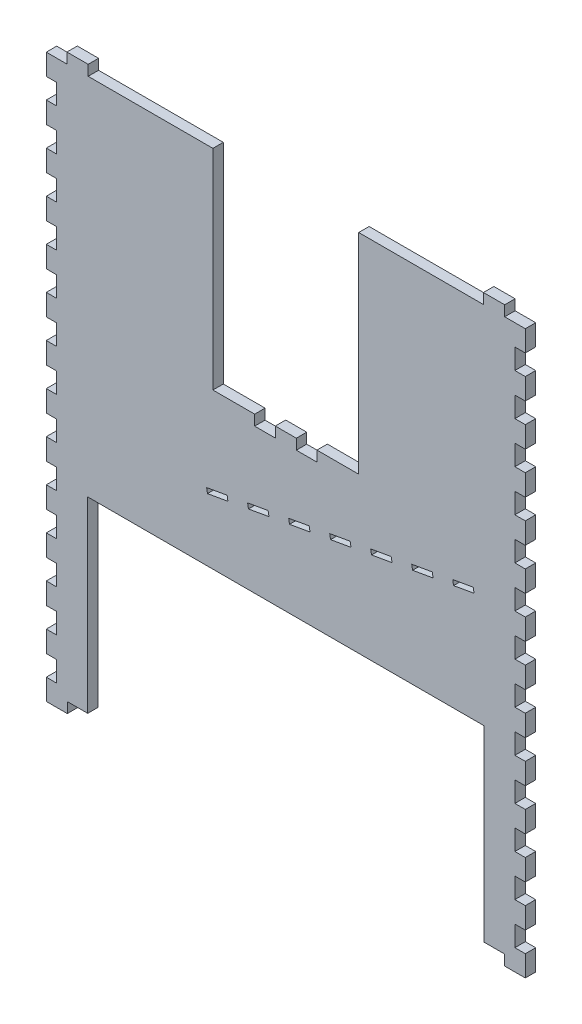
SolidWorks part; units mm, degrees
ref_plane "Front Plane" through (0, 0, 0) normal (0, 0, 1) x (1, 0, 0)
ref_plane "Top Plane" through (0, 0, 0) normal (0, 1, 0) x (1, 0, 0)
ref_plane "Right Plane" through (0, 0, 0) normal (1, 0, 0) x (0, 0, -1)
sketch "Sketch1" plane through (0, 0, 0) normal (0, 0, 1) x (1, 0, 0)
  line L0 (0, 0) -> (12.573, 0)
  line L1 (12.573, 0) -> (12.573, 6.35)
  line L2 (12.573, 6.35) -> (25.527, 6.35)
  line L3 (25.527, 6.35) -> (25.527, 0)
  line L4 (25.527, 0) -> (266.573, 0) construction
  line L5 (266.573, 0) -> (266.573, 6.35)
  line L6 (266.573, 6.35) -> (279.527, 6.35)
  line L7 (279.527, 6.35) -> (279.527, 0)
  line L8 (279.527, 0) -> (292.1, 0)
  line L9 (0, -12.827) -> (0, 0)
  line L10 (0, -12.827) -> (6.35, -12.827)
  line L11 (6.35, -12.827) -> (6.35, -25.273)
  line L12 (6.35, -25.273) -> (0, -25.273)
  line L13 (0, -25.273) -> (0, -38.227)
  line L14 (0, -38.227) -> (6.35, -38.227)
  line L15 (6.35, -38.227) -> (6.35, -50.673)
  line L16 (6.35, -50.673) -> (0, -50.673)
  line L17 (0, -50.673) -> (0, -63.627)
  line L18 (0, -63.627) -> (6.35, -63.627)
  line L19 (6.35, -63.627) -> (6.35, -76.073)
  line L20 (6.35, -76.073) -> (0, -76.073)
  line L21 (0, -76.073) -> (0, -89.027)
  line L22 (0, -89.027) -> (6.35, -89.027)
  line L23 (6.35, -89.027) -> (6.35, -101.473)
  line L24 (6.35, -101.473) -> (0, -101.473)
  line L25 (0, -101.473) -> (0, -114.427)
  line L26 (0, -114.427) -> (6.35, -114.427)
  line L27 (6.35, -114.427) -> (6.35, -126.873)
  line L28 (6.35, -126.873) -> (0, -126.873)
  line L29 (0, -126.873) -> (0, -139.827)
  line L30 (0, -139.827) -> (6.35, -139.827)
  line L31 (6.35, -139.827) -> (6.35, -152.273)
  line L32 (6.35, -152.273) -> (0, -152.273)
  line L33 (0, -152.273) -> (0, -165.227)
  line L34 (0, -165.227) -> (6.35, -165.227)
  line L35 (6.35, -165.227) -> (6.35, -177.673)
  line L36 (6.35, -177.673) -> (0, -177.673)
  line L37 (0, -177.673) -> (0, -190.627)
  line L38 (0, -190.627) -> (6.35, -190.627)
  line L39 (6.35, -190.627) -> (6.35, -203.073)
  line L40 (6.35, -203.073) -> (0, -203.073)
  line L41 (0, -203.073) -> (0, -216.027)
  line L42 (0, -216.027) -> (6.35, -216.027)
  line L43 (6.35, -216.027) -> (6.35, -228.473)
  line L44 (6.35, -228.473) -> (0, -228.473)
  line L45 (0, -228.473) -> (0, -241.427)
  line L46 (0, -241.427) -> (6.35, -241.427)
  line L47 (6.35, -241.427) -> (6.35, -253.873)
  line L48 (6.35, -253.873) -> (0, -253.873)
  line L49 (0, -253.873) -> (0, -266.827)
  line L50 (0, -266.827) -> (6.35, -266.827)
  line L51 (6.35, -266.827) -> (6.35, -279.273)
  line L52 (6.35, -279.273) -> (0, -279.273)
  line L53 (292.1, 0) -> (292.1, -12.827)
  line L54 (292.1, -12.827) -> (285.75, -12.827)
  line L55 (285.75, -12.827) -> (285.75, -25.273)
  line L56 (285.75, -25.273) -> (292.1, -25.273)
  line L57 (292.1, -25.273) -> (292.1, -38.227)
  line L58 (292.1, -38.227) -> (285.75, -38.227)
  line L59 (0, -342.9) -> (12.827, -342.9)
  line L60 (12.827, -342.9) -> (12.827, -336.55)
  line L61 (12.827, -336.55) -> (25.273, -336.55)
  line L62 (25.273, -336.55) -> (25.273, -342.9) construction
  line L63 (25.273, -342.9) -> (38.227, -342.9) construction
  line L64 (38.227, -342.9) -> (38.227, -336.55) construction
  line L65 (38.227, -336.55) -> (50.673, -336.55) construction
  line L66 (50.673, -336.55) -> (50.673, -342.9) construction
  line L67 (50.673, -342.9) -> (63.627, -342.9) construction
  line L68 (63.627, -342.9) -> (63.627, -336.55) construction
  line L69 (63.627, -336.55) -> (76.073, -336.55) construction
  line L70 (76.073, -336.55) -> (76.073, -342.9) construction
  line L71 (76.073, -342.9) -> (89.027, -342.9) construction
  line L72 (89.027, -342.9) -> (89.027, -336.55) construction
  line L73 (89.027, -336.55) -> (101.473, -336.55) construction
  line L74 (101.473, -336.55) -> (101.473, -342.9) construction
  line L75 (101.473, -342.9) -> (114.427, -342.9) construction
  line L76 (114.427, -342.9) -> (114.427, -336.55) construction
  line L77 (114.427, -336.55) -> (126.873, -336.55) construction
  line L78 (126.873, -336.55) -> (126.873, -342.9) construction
  line L79 (126.873, -342.9) -> (139.827, -342.9) construction
  line L80 (139.827, -342.9) -> (139.827, -336.55) construction
  line L81 (139.827, -336.55) -> (152.273, -336.55) construction
  line L82 (152.273, -336.55) -> (152.273, -342.9) construction
  line L83 (152.273, -342.9) -> (165.227, -342.9) construction
  line L84 (165.227, -342.9) -> (165.227, -336.55) construction
  line L85 (165.227, -336.55) -> (177.673, -336.55) construction
  line L86 (177.673, -336.55) -> (177.673, -342.9) construction
  line L87 (177.673, -342.9) -> (190.627, -342.9) construction
  line L88 (190.627, -342.9) -> (190.627, -336.55) construction
  line L89 (190.627, -336.55) -> (203.073, -336.55) construction
  line L90 (203.073, -336.55) -> (203.073, -342.9) construction
  line L91 (203.073, -342.9) -> (216.027, -342.9) construction
  line L92 (216.027, -342.9) -> (216.027, -336.55) construction
  line L93 (216.027, -336.55) -> (228.473, -336.55) construction
  line L94 (228.473, -336.55) -> (228.473, -342.9) construction
  line L95 (228.473, -342.9) -> (241.427, -342.9) construction
  line L96 (241.427, -342.9) -> (241.427, -336.55) construction
  line L97 (241.427, -336.55) -> (253.873, -336.55) construction
  line L98 (253.873, -336.55) -> (253.873, -342.9) construction
  line L99 (253.873, -342.9) -> (266.827, -342.9) construction
  line L100 (266.827, -342.9) -> (266.827, -336.55) construction
  line L101 (266.827, -336.55) -> (279.273, -336.55)
  line L102 (279.273, -336.55) -> (279.273, -342.9)
  line L103 (285.75, -38.227) -> (285.75, -50.673)
  line L104 (285.75, -50.673) -> (292.1, -50.673)
  line L105 (292.1, -50.673) -> (292.1, -63.627)
  line L106 (292.1, -63.627) -> (285.75, -63.627)
  line L107 (292.1, -342.9) -> (279.273, -342.9)
  line L108 (285.75, -63.627) -> (285.75, -76.073)
  line L109 (285.75, -76.073) -> (292.1, -76.073)
  line L110 (292.1, -76.073) -> (292.1, -89.027)
  line L111 (292.1, -89.027) -> (285.75, -89.027)
  line L112 (285.75, -89.027) -> (285.75, -101.473)
  line L113 (285.75, -101.473) -> (292.1, -101.473)
  line L114 (292.1, -101.473) -> (292.1, -114.427)
  line L115 (292.1, -114.427) -> (285.75, -114.427)
  line L116 (285.75, -114.427) -> (285.75, -126.873)
  line L117 (285.75, -126.873) -> (292.1, -126.873)
  line L118 (292.1, -126.873) -> (292.1, -139.827)
  line L119 (292.1, -139.827) -> (285.75, -139.827)
  line L120 (285.75, -139.827) -> (285.75, -152.273)
  line L121 (285.75, -152.273) -> (292.1, -152.273)
  line L122 (292.1, -152.273) -> (292.1, -165.227)
  line L123 (292.1, -165.227) -> (285.75, -165.227)
  line L124 (285.75, -165.227) -> (285.75, -177.673)
  line L125 (285.75, -177.673) -> (292.1, -177.673)
  line L126 (292.1, -177.673) -> (292.1, -190.627)
  line L127 (292.1, -190.627) -> (285.75, -190.627)
  line L128 (285.75, -190.627) -> (285.75, -203.073)
  line L129 (285.75, -203.073) -> (292.1, -203.073)
  line L130 (292.1, -203.073) -> (292.1, -216.027)
  line L131 (292.1, -216.027) -> (285.75, -216.027)
  line L132 (285.75, -216.027) -> (285.75, -228.473)
  line L133 (285.75, -228.473) -> (292.1, -228.473)
  line L134 (292.1, -228.473) -> (292.1, -241.427)
  line L135 (292.1, -241.427) -> (285.75, -241.427)
  line L136 (285.75, -241.427) -> (285.75, -253.873)
  line L137 (285.75, -253.873) -> (292.1, -253.873)
  line L138 (292.1, -253.873) -> (292.1, -266.827)
  line L139 (292.1, -266.827) -> (285.75, -266.827)
  line L140 (285.75, -266.827) -> (285.75, -279.273)
  line L141 (285.75, -279.273) -> (292.1, -279.273)
  line L142 (292.1, -279.273) -> (292.1, -292.227)
  line L143 (146.05, 0) -> (146.05, -285.75) construction
  line L144 (0, -279.273) -> (0, -292.227)
  line L145 (0, -292.227) -> (6.35, -292.227)
  line L146 (6.35, -292.227) -> (6.35, -304.673)
  line L147 (6.35, -304.673) -> (0, -304.673)
  line L148 (0, -304.673) -> (0, -317.627)
  line L149 (0, -317.627) -> (6.35, -317.627)
  line L150 (6.35, -317.627) -> (6.35, -330.073)
  line L151 (6.35, -330.073) -> (0, -330.073)
  line L152 (260.8705, -155.3517) -> (248.3634, -157.557)
  line L153 (260.8705, -155.3517) -> (260.35, -152.4)
  line L154 (248.3634, -157.557) -> (247.8429, -154.6053)
  line L155 (260.35, -152.4) -> (247.8429, -154.6053)
  line L156 (235.8563, -159.7623) -> (223.3493, -161.9677)
  line L157 (235.8563, -159.7623) -> (235.3359, -156.8107)
  line L158 (223.3493, -161.9677) -> (222.8288, -159.016)
  line L159 (235.3359, -156.8107) -> (222.8288, -159.016)
  line L160 (152.4635, -127.635) -> (152.4635, -133.985)
  line L161 (127.0635, -127.635) -> (139.6365, -127.635) construction
  line L162 (127.0635, -127.635) -> (127.0635, -133.985)
  line L163 (127.0635, -133.985) -> (139.6365, -133.985)
  line L164 (139.6365, -127.635) -> (139.6365, -133.985)
  line L165 (165.0365, -133.985) -> (152.4635, -133.985)
  line L166 (165.0365, -127.635) -> (165.0365, -133.985)
  line L167 (165.0365, -127.635) -> (152.4635, -127.635) construction
  line L168 (210.8422, -164.173) -> (198.3352, -166.3783)
  line L169 (210.8422, -164.173) -> (210.3218, -161.2213)
  line L170 (198.3352, -166.3783) -> (197.8147, -163.4267)
  line L171 (210.3218, -161.2213) -> (197.8147, -163.4267)
  line L172 (185.8281, -168.5837) -> (173.321, -170.789)
  line L173 (0, -330.073) -> (0, -342.9)
  line L174 (292.1, -292.227) -> (285.75, -292.227)
  line L175 (285.75, -292.227) -> (285.75, -304.673)
  line L176 (285.75, -304.673) -> (292.1, -304.673)
  line L177 (292.1, -304.673) -> (292.1, -317.627)
  line L178 (292.1, -317.627) -> (285.75, -317.627)
  line L179 (285.75, -317.627) -> (285.75, -330.073)
  line L180 (285.75, -330.073) -> (292.1, -330.073)
  line L181 (185.8281, -168.5837) -> (185.3076, -165.632)
  line L182 (173.321, -170.789) -> (172.8006, -167.8373)
  line L183 (185.3076, -165.632) -> (172.8006, -167.8373)
  line L184 (160.814, -172.9943) -> (148.3069, -175.1997)
  line L185 (160.814, -172.9943) -> (160.2935, -170.0427)
  line L186 (148.3069, -175.1997) -> (147.7865, -172.248)
  line L187 (160.2935, -170.0427) -> (147.7865, -172.248)
  line L188 (135.7999, -177.405) -> (123.2928, -179.6103)
  line L189 (135.7999, -177.405) -> (135.2794, -174.4533)
  line L190 (123.2928, -179.6103) -> (122.7724, -176.6587)
  line L191 (135.2794, -174.4533) -> (122.7724, -176.6587)
  line L192 (110.7858, -181.8156) -> (98.2787, -184.021)
  line L193 (292.1, -330.073) -> (292.1, -342.9)
  line L194 (110.7858, -181.8156) -> (110.2653, -178.864)
  line L195 (98.2787, -184.021) -> (97.7582, -181.0693)
  line L196 (110.2653, -178.864) -> (97.7582, -181.0693)
  line L197 (279.273, -342.9) -> (292.227, -342.9) [skipped]
  line L198 (292.1, -330.073) -> (292.1, -343.027) [skipped]
  line L199 (0, -330.073) -> (0, -343.027) [skipped]
  line L200 (6.35, -330.073) -> (0, -330.073) [skipped]
  line L201 (152.4635, -127.635) -> (139.6365, -127.635)
  line L202 (127.0635, -127.635) -> (101.6, -127.635)
  line L203 (101.6, -127.635) -> (101.6, 0)
  line L204 (101.6, 0) -> (25.527, 0)
  line L205 (165.0365, -127.635) -> (190.5, -127.635)
  line L206 (190.5, -127.635) -> (190.5, 0)
  line L207 (190.5, 0) -> (266.573, 0)
  line L208 (266.827, -336.55) -> (266.827, -222.25)
  line L209 (266.827, -222.25) -> (25.273, -222.25)
  line L210 (25.273, -222.25) -> (25.273, -336.55)
  dimension "D2" = 12.954
  dimension "D3" = 6.35
  dimension "D4" = 6.35
  dimension "D5" = 12.573
  dimension "D6" = 12.954
  dimension "D7" = 12.573
  dimension "D8" = 12.827
  dimension "D9" = 12.446
  dimension "D10" = 6.35
  dimension "D11" = 6.35
  dimension "D12" = 12.954
  dimension "D14" = 12.827
  dimension "D15" = 12.827
  dimension "D16" = 12.446
  dimension "D17" = 12.954
  dimension "D18" = 6.35
  dimension "D19" = 6.35
  dimension "D21" = 12.446
  dimension "D22" = 12.954
  dimension "D23" = 6.35
  dimension "D24" = 6.35
  dimension "D25" = 13
  dimension "D27" = 12.827
  dimension "D28" = 127.635
  dimension "D29" = 12.573
  dimension "D30" = 6.35
  dimension "D31" = 241.046
  dimension "D32" = 12.7
  dimension "D33" = 10
  dimension "D34" = 6.4135
  dimension "D35" = 88.9
  dimension "D26" = 2.9972
  dimension "D36" = 152.4
  dimension "D37" = 25.4
  dimension "D38" = 25.4635
  dimension "D39" = 114.3
  dimension "D13" = 13
  dimension "D20" = 11
extrude "Boss-Extrude1" add sketch "Sketch1" along normal blind 6.35
